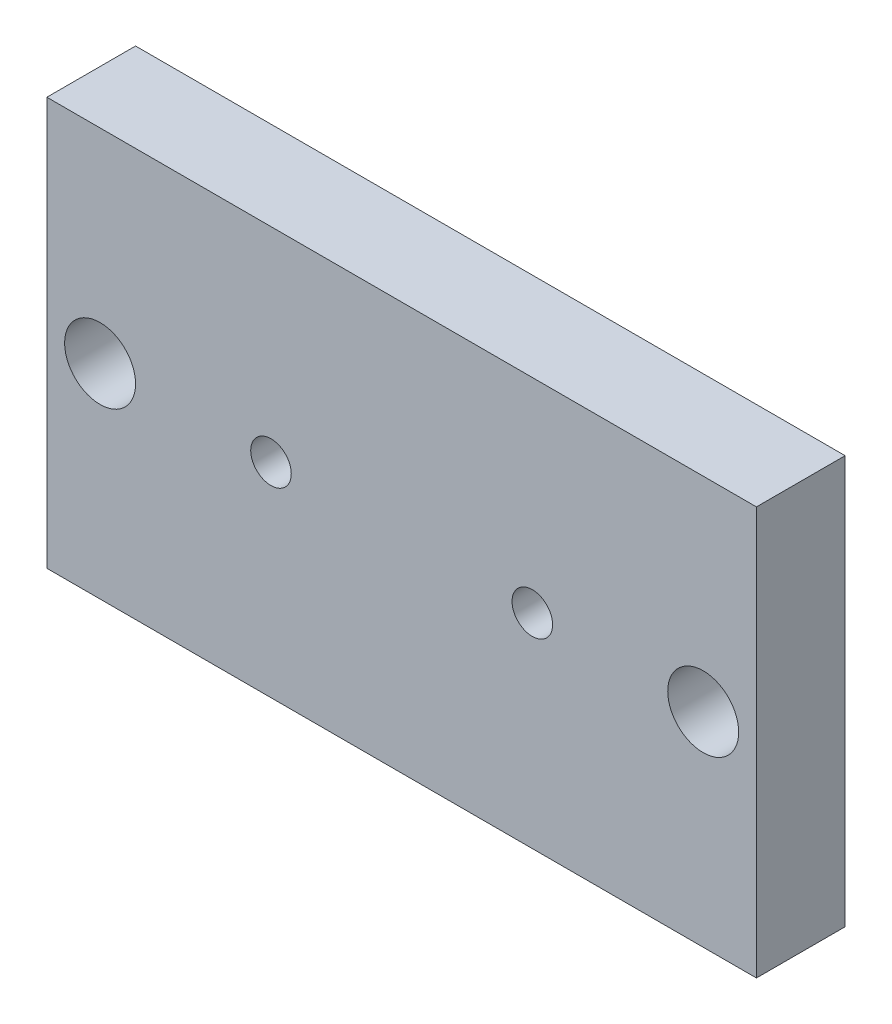
SolidWorks part; units mm, degrees
ref_plane "Front Plane" through (0, 0, 0) normal (0, 0, 1) x (1, 0, 0)
ref_plane "Top Plane" through (0, 0, 0) normal (0, 1, 0) x (1, 0, 0)
ref_plane "Right Plane" through (0, 0, 0) normal (1, 0, 0) x (0, 0, -1)
sketch "Sketch1" plane through (0, 0, 0) normal (0, 0, 1) x (1, 0, 0)
  line L1 (-20, 11.5) -> (20, 11.5)
  line L2 (-20, 11.5) -> (-20, -11.5)
  line L3 (-20, -11.5) -> (20, -11.5)
  line L4 (20, 11.5) -> (20, -11.5)
  dimension "D1" = 40
  dimension "D2" = 23
  dimension "D3" = 11.5
  dimension "D4" = 20
extrude "Boss-Extrude1" add sketch "Sketch1" along normal blind 5
sketch "Sketch2" plane through (0, 0, 0) normal (0, 0, -1) x (-1, 0, 0)
  line L0 (0, 0) -> (21.717, 0) construction
  line L1 (0, 0) -> (0, 9.5821) construction
  circle A1 centre (-17, 0) radius 2
  circle A3 centre (-7.366, 0) radius 1.143
  circle A5 centre (7.366, 0) radius 1.143
  circle A7 centre (17, 0) radius 2
  dimension "D3" = 4
  dimension "D4" = 2.286
  dimension "D5" = 2.286
  dimension "D6" = 4
  dimension "D1" = 14.732
  dimension "D2" = 9.634
  dimension "D7" = 7.366
  dimension "D8" = 17
extrude "Cut-Extrude1" cut sketch "Sketch2" against normal blind 10
